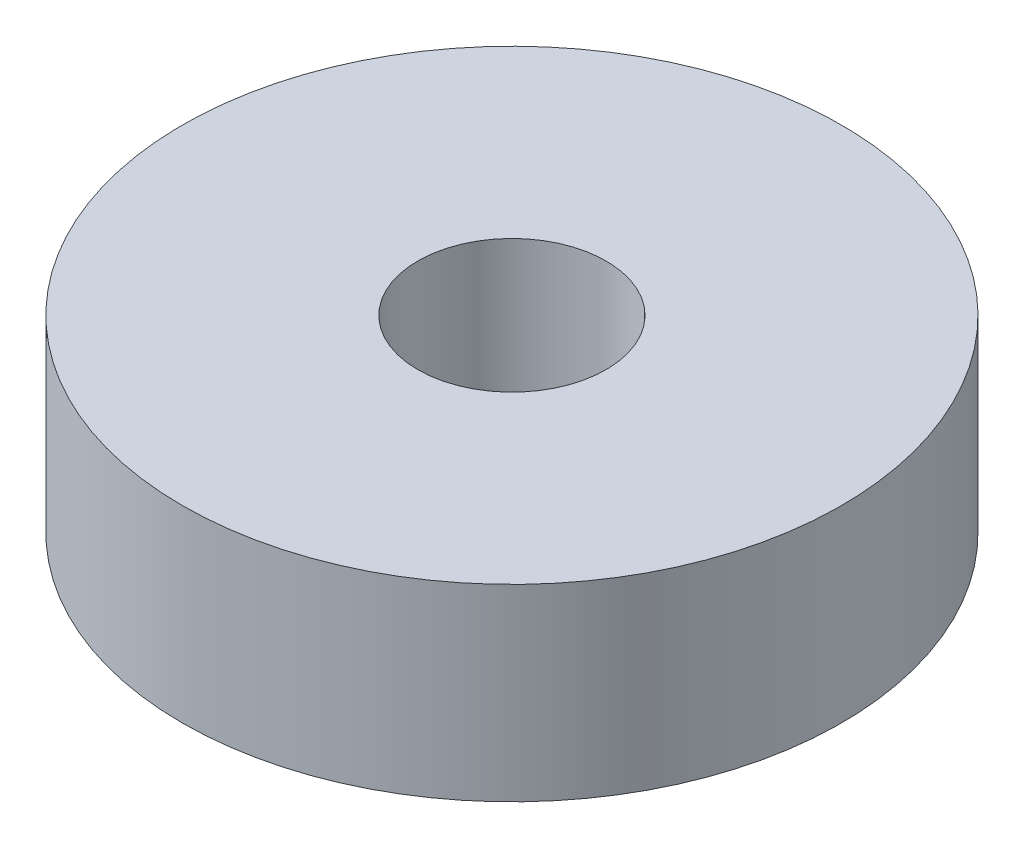
SolidWorks part; units mm, degrees
material "1060 合金"
ref_plane "前视基准面" through (0, 0, 0) normal (0, 0, 1) x (1, 0, 0)
ref_plane "上视基准面" through (0, 0, 0) normal (0, 1, 0) x (1, 0, 0)
ref_plane "右视基准面" through (0, 0, 0) normal (1, 0, 0) x (0, 0, -1)
sketch "草图1" plane through (0, 0, 0) normal (0, 1, 0) x (1, 0, 0)
  circle A0 centre (0, 0) radius 2
  circle A1 centre (0, 0) radius 7
  dimension "D1" = 4
  dimension "D2" = 14
extrude "凸台-拉伸1" add sketch "草图1" along normal blind 4
